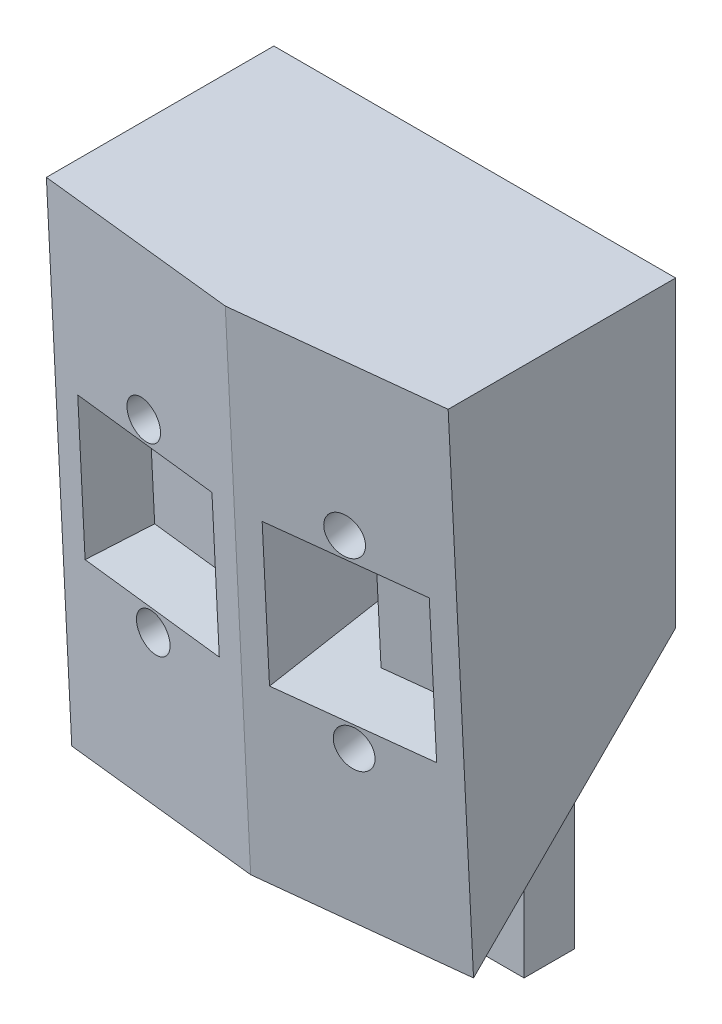
SolidWorks part; units mm, degrees
ref_plane "Front Plane" through (0, 0, 0) normal (0, 0, 1) x (1, 0, 0)
ref_plane "Top Plane" through (0, 0, 0) normal (0, 1, 0) x (1, 0, 0)
ref_plane "Right Plane" through (0, 0, 0) normal (1, 0, 0) x (0, 0, -1)
sketch "Sketch1" plane through (0, 0, 0) normal (0, 1, 0) x (1, 0, 0)
  line L0 (-20.1992, 2.2122) -> (0, 0)
  line L1 (0, 0) -> (-53.1168, 0) construction
  line L2 (0, 0) -> (0, 52.0153) construction
  line L3 (-20.1992, 2.2122) -> (-20.1992, 22.5322)
  line L4 (-20.1992, 22.5322) -> (20.1992, 22.5322)
  line L5 (20.1992, 2.2122) -> (0, 0)
  line L6 (20.1992, 2.2122) -> (20.1992, 22.5322)
  point P8 (0, 22.5322)
  dimension "D1" = 6.25
  dimension "D2" = 20.32
  dimension "D3" = 20.32
extrude "Boss-Extrude1" add sketch "Sketch1" against normal blind 50.8
draft "Draft1" type of draft neutral plane draft angle 2.86 faces to draft 2 face at (10.0996, -25.4, -1.1061) face at (-10.0996, -25.4, -1.1061) neutral plane through (0, -50.8, 0) neutral plane normal (0, -1, 0) parameters "D1"=2.86
sketch "Sketch2" plane through (-20.1992, 0, 0) normal (-1, 0, 0) x (0, 0, 1)
  line L0 (-22.5322, -30.48) -> (-2.2122, -50.8)
  line L1 (-22.5322, -50.8) -> (-22.5322, 0) construction
  line L2 (-2.2122, -50.8) -> (-22.5322, -50.8)
  line L3 (-22.5322, -50.8) -> (-2.2122, -50.8) construction
  line L4 (-22.5322, -50.8) -> (-22.5322, -30.48)
  dimension "D1" = 45
extrude "Cut-Extrude1" cut sketch "Sketch2" against normal blind 10.16
ref_plane "Plane1" through (0, 0, 0) normal (-1, 0, 0) x (0, 0, 1)
mirror "Mirror1" about plane through (0, 0, 0) normal (-1, 0, 0) of "Cut-Extrude1"
sketch "Sketch3" plane through (0, -50.8, 0) normal (0, -1, 0) x (1, 0, 0)
  line L0 (10.0392, -2.2122) -> (10.0392, -22.5322) construction
  line L1 (-10.0392, -22.5322) -> (10.0392, -22.5322)
  line L2 (-10.0392, -22.5322) -> (-10.0392, -17.4522)
  line L3 (-10.0392, -17.4522) -> (10.0392, -17.4522)
  line L4 (10.0392, -22.5322) -> (10.0392, -17.4522)
  dimension "D1" = 5.08
extrude "Boss-Extrude2" add sketch "Sketch3" along normal blind 12.7
sketch "Sketch4" plane through (-0.2756, -0.1265, 2.5165) normal (-0.1087, -0.0499, 0.9928) x (0.9941, -0.0055, 0.1086)
  line L0 (-9.8826, 0.0726) -> (-9.8826, -50.7915) construction
  line L1 (-20.0425, 0.0171) -> (0.2772, 0.1281) construction
  line L2 (-20.0425, -50.847) -> (0.2772, -50.736) construction
  line L3 (-9.8826, -15.8344) -> (-9.8826, -34.8844) construction
  line L4 (-7.3426, -17.9934) -> (-7.3426, -32.7254)
  line L5 (-17.5026, -32.7254) -> (-2.2626, -32.7254) construction
  line L6 (-17.5026, -32.7254) -> (-17.5026, -17.9934) construction
  line L7 (-17.5026, -17.9934) -> (-2.2626, -17.9934) construction
  line L8 (-2.2626, -32.7254) -> (-2.2626, -17.9934)
  line L9 (-17.5026, -32.7254) -> (-2.2626, -17.9934) construction
  line L10 (-17.5026, -17.9934) -> (-2.2626, -32.7254) construction
  line L11 (-2.2626, -17.9934) -> (-7.3426, -17.9934)
  line L12 (-7.3426, -32.7254) -> (-2.2626, -32.7254)
  circle A0 centre (-9.8826, -15.8344) radius 1.905
  circle A1 centre (-9.8826, -34.8844) radius 1.905
  point P10 (-9.8826, -25.3594)
  point P11 (-9.8826, -25.3594)
  point P12 (-9.8826, -25.3594)
  point P17 (-9.8826, -17.7394)
  dimension "D1" = 3.81
  dimension "D2" = 19.05
  dimension "D3" = 15.24
  dimension "D4" = 0.254
  dimension "D5" = 5.08
extrude "Cut-Extrude2" cut sketch "Sketch4" along normal through all and the other way through all
sketch "Sketch5" plane through (-0.2756, -0.1265, 2.5165) normal (-0.1087, -0.0499, 0.9928) x (0.9941, -0.0055, 0.1086)
  line L0 (-9.8826, 0.0726) -> (-9.8826, -50.7915) construction
  line L3 (-9.8826, -15.8344) -> (-9.8826, -34.8844) construction
  line L5 (-17.5026, -32.7254) -> (-2.2626, -32.7254)
  line L6 (-17.5026, -32.7254) -> (-17.5026, -17.9934)
  line L7 (-17.5026, -17.9934) -> (-2.2626, -17.9934)
  line L8 (-2.2626, -32.7254) -> (-2.2626, -17.9934)
  line L9 (-17.5026, -32.7254) -> (-2.2626, -17.9934) construction
  line L10 (-17.5026, -17.9934) -> (-2.2626, -32.7254) construction
  line L13 (-20.0425, -50.847) -> (0.2772, -50.736) construction
  line L14 (-20.0425, 0.0171) -> (0.2772, 0.1281) construction
  circle A0 centre (-9.8826, -15.8344) radius 1.905 construction
  circle A1 centre (-9.8826, -34.8844) radius 1.905 construction
  point P2 (0, 0)
  point P5 (0, 0)
  point P10 (-9.8826, -25.3594)
  point P11 (-9.8826, -25.3594)
  point P12 (-9.8826, -25.3594)
  point P17 (-9.8826, -17.7394)
  point P18 (-17.5026, -17.7394)
  dimension "D1" = 3.81
  dimension "D2" = 19.05
  dimension "D3" = 15.24
  dimension "D4" = 0.254
extrude "Cut-Extrude3" cut sketch "Sketch5" against normal blind 6.35
mirror "Mirror2" about plane through (0, 0, 0) normal (-1, 0, 0) of "Cut-Extrude2", "Cut-Extrude3"
